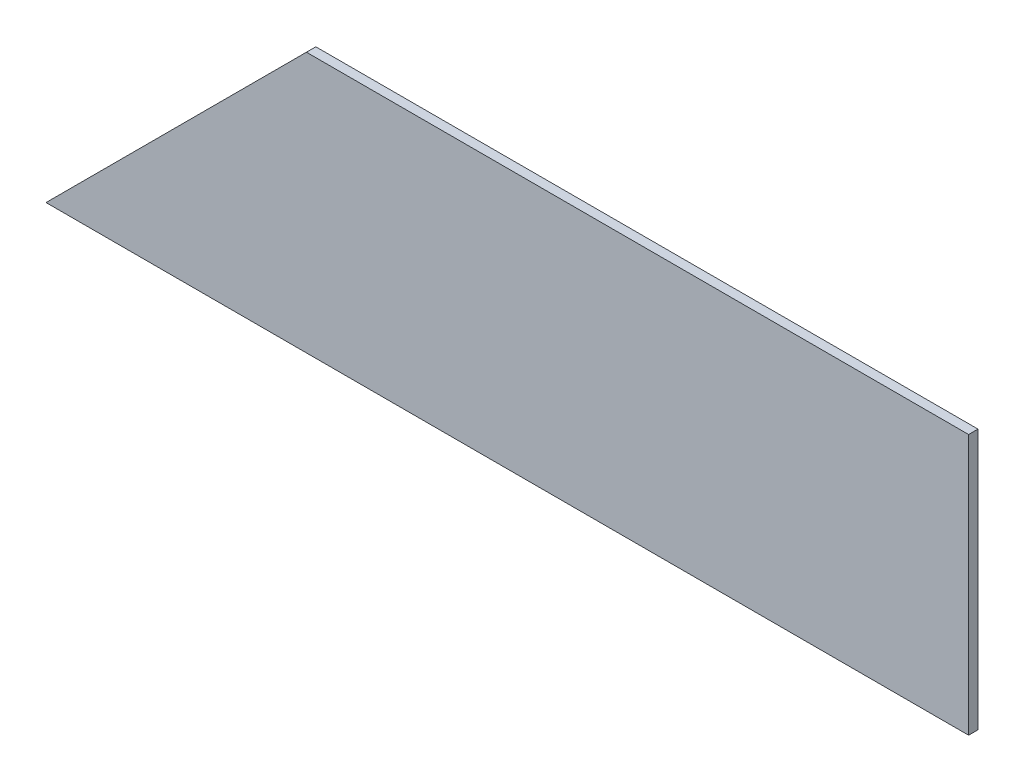
SolidWorks part; units mm, degrees
material "A-Glass Fiber"
ref_plane "Front Plane" through (0, 0, 0) normal (0, 0, 1) x (1, 0, 0)
ref_plane "Top Plane" through (0, 0, 0) normal (0, 1, 0) x (1, 0, 0)
ref_plane "Right Plane" through (0, 0, 0) normal (1, 0, 0) x (0, 0, -1)
sketch "Sketch1" plane through (0, 0, 0) normal (0, 0, 1) x (1, 0, 0)
  line L0 (416.4665, 276.8092) -> (711.1767, 276.8092) construction
  line L1 (711.1767, 276.8092) -> (711.1767, 360) construction
  line L2 (711.1767, 360) -> (499.6574, 360) construction
  line L3 (499.6574, 360) -> (416.4665, 276.8092) construction
  line L4 (416.4665, 276.8092) -> (711.1767, 276.8092)
  line L5 (711.1767, 276.8092) -> (711.1767, 360)
  line L6 (711.1767, 360) -> (499.6574, 360)
  line L7 (499.6574, 360) -> (416.4665, 276.8092)
extrude "Boss-Extrude1" add sketch "Sketch1" against normal blind 3
